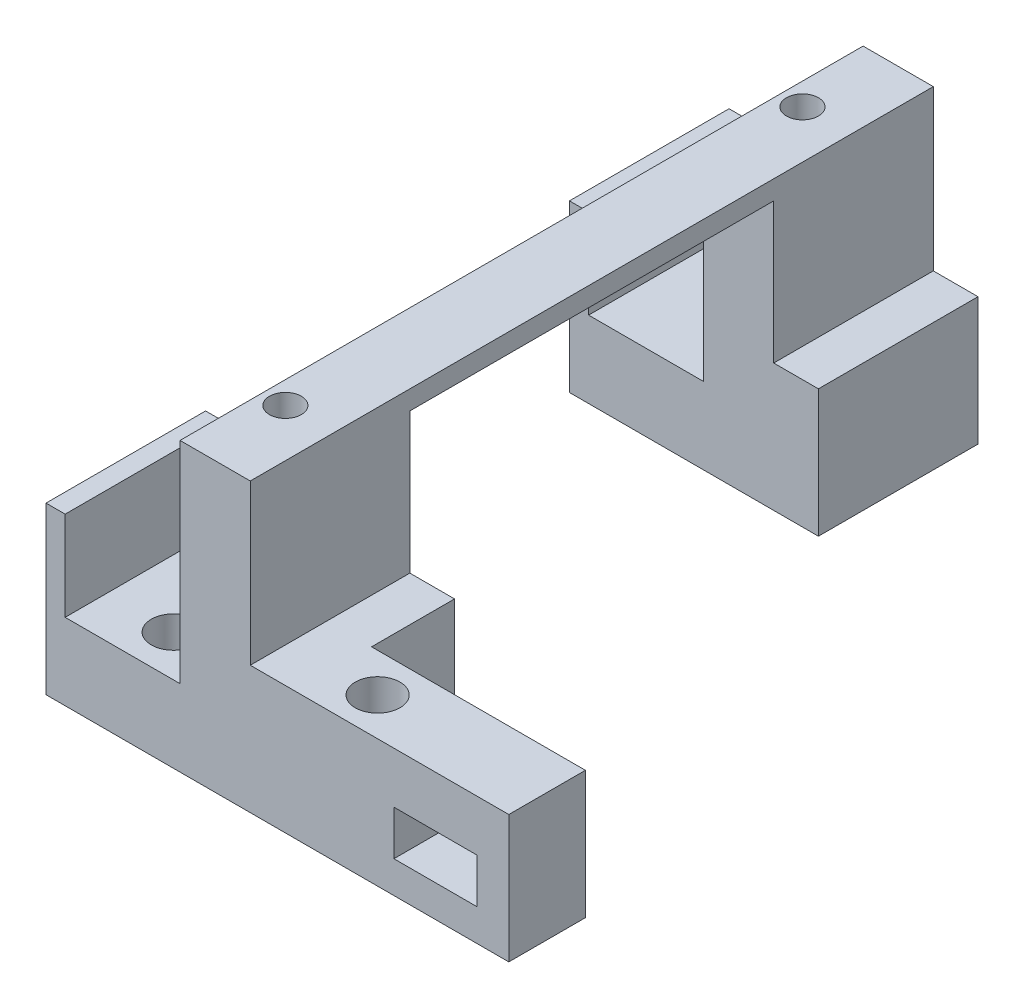
SolidWorks part; units mm, degrees
ref_plane "Alzado" through (0, 0, 0) normal (0, 0, 1) x (1, 0, 0)
ref_plane "Planta" through (0, 0, 0) normal (0, 1, 0) x (1, 0, 0)
ref_plane "Vista lateral" through (0, 0, 0) normal (1, 0, 0) x (0, 0, -1)
sketch "Croquis1" plane through (0, 0, 0) normal (0, 0, 1) x (1, 0, 0)
  line L0 (0, 0) -> (39, 0)
  line L1 (39, 0) -> (39, 20)
  line L2 (39, 20) -> (32, 20)
  line L3 (32, 20) -> (32, 45)
  line L4 (32, 45) -> (21, 45)
  line L5 (21, 45) -> (21, 12)
  line L6 (21, 12) -> (3, 12)
  line L7 (3, 12) -> (3, 26)
  line L8 (3, 26) -> (0, 26)
  line L9 (0, 26) -> (0, 0)
  dimension "D1" = 39
  dimension "D2" = 25
  dimension "D3" = 12
  dimension "D4" = 11
  dimension "D5" = 3
  dimension "D6" = 18
  dimension "D7" = 14
  dimension "D8" = 20
extrude "Saliente-Extruir1" add sketch "Croquis1" along normal blind 107
sketch "Croquis3" plane through (0, 0, 0) normal (-1, 0, 0) x (0, 0, 1)
  line L0 (25, 0) -> (25, 42)
  line L1 (107, 0) -> (0, 0) construction
  line L2 (25, 42) -> (82, 42)
  line L3 (82, 42) -> (82, 0)
  line L4 (82, 0) -> (25, 0)
  line L5 (0, 26) -> (0, 0) construction
  line L6 (107, 26) -> (107, 0) construction
  line L8 (107, 45) -> (0, 45) construction
  dimension "D1" = 25
  dimension "D2" = 25
  dimension "D3" = 3
extrude "Cortar-Extruir1" cut sketch "Croquis3" against normal up to surface (39 mm away) up to face at (39, 10, 53.5)
sketch "Croquis2" plane through (0, 45, 0) normal (0, 1, 0) x (1, 0, 0)
  line L0 (32, -107) -> (21, -107) construction
  line L2 (21, -107) -> (21, 0) construction
  line L3 (32, 0) -> (21, 0) construction
  circle A0 centre (24.5, -94) radius 2.5
  circle A1 centre (24.5, -13) radius 2.5
  dimension "D1" = 5
  dimension "D2" = 13
  dimension "D4" = 5
  dimension "D3" = 3.5
  dimension "D5" = 3.5
  dimension "D6" = 13
extrude "Cortar-Extruir2" cut sketch "Croquis2" against normal up to next
sketch "Croquis4" plane through (0, 12, 0) normal (0, 1, 0) x (1, 0, 0)
  line L0 (21, -107) -> (3, -107) construction
  line L1 (21, -107) -> (21, -82) construction
  line L2 (21, 0) -> (3, 0) construction
  line L3 (21, -25) -> (21, 0) construction
  circle A0 centre (13.5, -100.5) radius 3.5
  circle A1 centre (13.5, -6.5) radius 3.5
  dimension "D1" = 7
  dimension "D4" = 7
  dimension "D6" = 7.5
  dimension "D2" = 6.5
  dimension "D3" = 7.5
  dimension "D5" = 6.5
extrude "Cortar-Extruir3" cut sketch "Croquis4" against normal up to next
sketch "Croquis5" plane through (39, 0, 0) normal (1, 0, 0) x (0, 0, -1)
  line L0 (-107, 0) -> (-95, 0)
  line L1 (-107, 0) -> (-82, 0) construction
  line L2 (-95, 0) -> (-95, 20)
  line L3 (-107, 20) -> (-82, 20) construction
  line L4 (-95, 20) -> (-107, 20)
  line L5 (-107, 20) -> (-107, 0)
  dimension "D1" = 12
extrude "Saliente-Extruir2" add sketch "Croquis5" along normal blind 33.5
sketch "Croquis7" plane through (0, 20, 0) normal (0, 1, 0) x (1, 0, 0)
  line L0 (39, -95) -> (39, -82) construction
  circle A0 centre (46, -101.0539) radius 3.5
  dimension "D1" = 7
  dimension "D2" = 7
extrude "Cortar-Extruir4" cut sketch "Croquis7" against normal up to next
sketch "Croquis8" plane through (0, 0, 107) normal (0, 0, 1) x (1, 0, 0)
  line L0 (0, 0) -> (72.5, 0) construction
  line L1 (54.5, 12) -> (67.5, 12)
  line L2 (54.5, 12) -> (54.5, 5)
  line L3 (54.5, 5) -> (67.5, 5)
  line L4 (67.5, 12) -> (67.5, 5)
  line L7 (72.5, 20) -> (72.5, 0) construction
  dimension "D1" = 5
  dimension "D2" = 13
  dimension "D3" = 7
  dimension "D4" = 5
extrude "Cortar-Extruir5" cut sketch "Croquis8" against normal up to next
